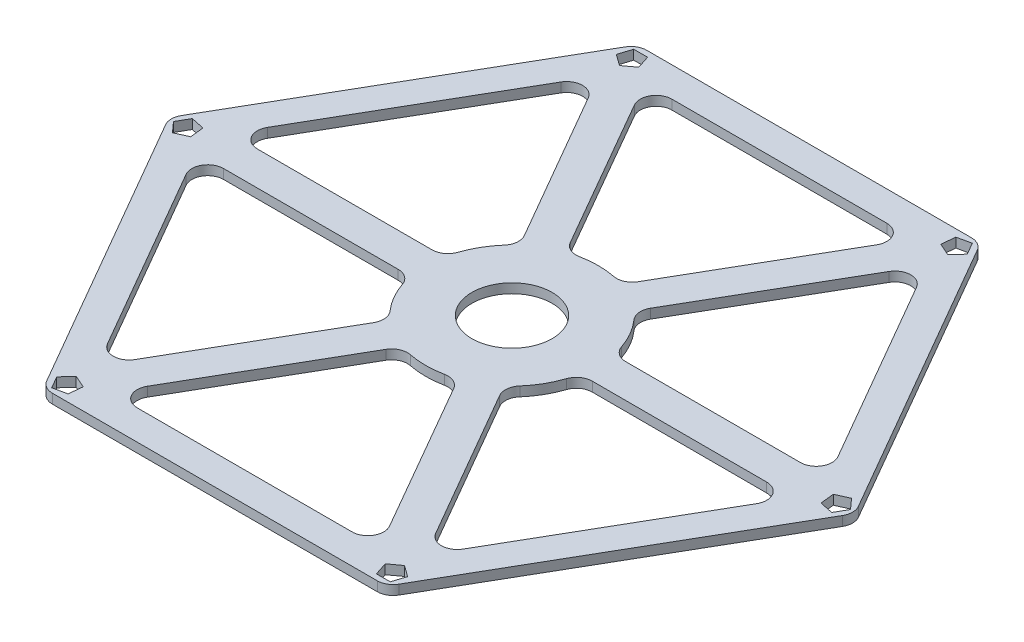
SolidWorks part; units mm, degrees
ref_plane "Front Plane" through (0, 0, 0) normal (0, 0, 1) x (1, 0, 0)
ref_plane "Top Plane" through (0, 0, 0) normal (0, 1, 0) x (1, 0, 0)
ref_plane "Right Plane" through (0, 0, 0) normal (1, 0, 0) x (0, 0, -1)
sketch "Sketch1" plane through (0, 0, 0) normal (0, 1, 0) x (1, 0, 0)
  line L0 (-30.85, 53.4338) -> (-30.85, 42.7905) construction
  line L1 (-32.5, 56.2917) -> (-65, 0)
  line L2 (-65, 0) -> (-32.5, -56.2917)
  line L3 (-32.5, -56.2917) -> (32.5, -56.2917)
  line L4 (32.5, -56.2917) -> (65, 0)
  line L5 (65, 0) -> (32.5, 56.2917)
  line L6 (32.5, 56.2917) -> (-32.5, 56.2917)
  line L7 (-31.0984, 47.4555) -> (-56.6469, 3.2043)
  line L8 (-56.6469, -3.2043) -> (-31.0984, -47.4555)
  line L9 (-25.5484, -50.6598) -> (3, -50.6598)
  line L10 (31.0984, -47.4555) -> (56.6468, -3.2044)
  line L11 (56.6469, 3.2043) -> (31.0985, 47.4554)
  line L12 (25.5484, 50.6598) -> (-25.5483, 50.6598)
  line L13 (-30.85, 53.4338) -> (-61.7, 0) construction
  line L14 (-61.7, 0) -> (-30.85, -53.4338) construction
  line L15 (-30.85, -53.4338) -> (30.85, -53.4338) construction
  line L16 (30.85, -53.4338) -> (61.7, 0) construction
  line L17 (61.7, 0) -> (30.85, 53.4338) construction
  line L18 (30.85, 53.4338) -> (-30.85, 53.4338) construction
  line L50 (28.9265, 52.3155) -> (31.3192, 51.2589)
  line L51 (-30.8433, 51.2089) -> (-28.7319, 52.7526)
  line L52 (-28.7319, 52.7526) -> (-29.5477, 55.2377)
  line L58 (-31.0984, 47.4555) -> (-10.8026, 12.302)
  line L60 (25.5484, 50.6598) -> (5.2525, 15.5063)
  line L66 (56.6469, 3.2043) -> (16.0551, 3.2043)
  line L72 (31.0984, -47.4555) -> (10.8026, -12.302)
  line L78 (-25.5484, -50.6598) -> (-5.2525, -15.5063)
  line L84 (-56.6469, -3.2043) -> (-16.0551, -3.2043)
  line L89 (-5.298, 15.4908) -> (-25.5483, 50.6598)
  line L91 (-29.5477, 55.2377) -> (-32.1632, 55.2298)
  line L92 (10.7664, 12.3336) -> (31.0985, 47.4554)
  line L94 (-32.1632, 55.2298) -> (-32.9639, 52.7398)
  line L95 (16.0644, -3.1572) -> (56.6468, -3.2044)
  line L97 (-32.9639, 52.7398) -> (-30.8433, 51.2089)
  line L98 (5.298, -15.4908) -> (25.5483, -50.6598)
  line L100 (31.3192, 51.2589) -> (33.0634, 53.2079)
  line L101 (-10.8026, -12.302) -> (-31.0984, -47.4555)
  line L103 (33.0634, 53.2079) -> (31.7488, 55.4691)
  line L104 (-16.0551, 3.2043) -> (-56.6469, 3.2043)
  line L106 (31.7488, 55.4691) -> (29.1921, 54.9175)
  line L107 (29.1921, 54.9175) -> (28.9265, 52.3155)
  line L108 (59.7698, 1.1066) -> (60.0511, -1.4938)
  line L109 (60.0511, -1.4938) -> (62.6111, -2.0298)
  line L110 (62.6111, -2.0298) -> (63.912, 0.2393)
  line L111 (63.912, 0.2393) -> (62.156, 2.1777)
  line L112 (62.156, 2.1777) -> (59.7698, 1.1066)
  line L113 (30.8433, -51.2089) -> (28.7319, -52.7526)
  line L114 (28.7319, -52.7526) -> (29.5477, -55.2377)
  line L115 (29.5477, -55.2377) -> (32.1632, -55.2298)
  line L116 (32.1632, -55.2298) -> (32.9639, -52.7398)
  line L117 (32.9639, -52.7398) -> (30.8433, -51.2089)
  line L118 (-28.9265, -52.3155) -> (-31.3192, -51.2589)
  line L119 (-31.3192, -51.2589) -> (-33.0634, -53.2079)
  line L120 (-33.0634, -53.2079) -> (-31.7488, -55.4691)
  line L121 (-31.7488, -55.4691) -> (-29.1921, -54.9175)
  line L122 (-29.1921, -54.9175) -> (-28.9265, -52.3155)
  line L123 (-59.7698, -1.1066) -> (-60.0511, 1.4938)
  line L124 (-60.0511, 1.4938) -> (-62.6111, 2.0298)
  line L125 (-62.6111, 2.0298) -> (-63.912, -0.2393)
  line L126 (-63.912, -0.2393) -> (-62.156, -2.1777)
  line L127 (-62.156, -2.1777) -> (-59.7698, -1.1066)
  line L128 (0, 0) -> (0, -56.2917) construction
  line L134 (3, -50.6598) -> (25.5483, -50.6598)
  circle A0 centre (0, 0) radius 56.2917 construction
  circle A1 centre (0, 0) radius 50.6598 construction
  circle A2 centre (0, 0) radius 53.4338 construction
  circle A3 centre (-30.85, 53.4338) radius 1.8 construction
  arc A4 (-10.8026, 12.302) -> (-16.0551, 3.2043) centre (0, 0) ccw
  arc A5 (5.2525, 15.5063) -> (-5.298, 15.4908) centre (0, 0) ccw
  arc A6 (16.0551, 3.2043) -> (10.7664, 12.3336) centre (0, 0) ccw
  arc A7 (10.8026, -12.302) -> (16.0644, -3.1572) centre (0, 0) ccw
  arc A8 (-5.2525, -15.5063) -> (3.0697, -16.0814) centre (0, 0) ccw
  arc A9 (-16.0551, -3.2043) -> (-10.8026, -12.302) centre (0, 0) ccw
  arc A10 (3.0697, -16.0814) -> (5.298, -15.4908) centre (0, 0) ccw
  point P53 (0, 0)
  point P58 (-0.0078, -0.0152)
  point P70 (0, 0)
  point P87 (0, 0)
  dimension "D1" = 65
  dimension "D2" = 30
  dimension "D3" = 3.3
  dimension "D4" = 6
  dimension "D7" = 6
extrude "Boss-Extrude1" add sketch "Sketch1" along normal blind 1.8
fillet "Fillet1" radius 3 6 edges at (-65, 0.9, 0) (-32.5, 0.9, 56.2917) (32.5, 0.9, 56.2917) (65, 0.9, 0) (32.5, 0.9, -56.2917) (-32.5, 0.9, -56.2917)
sketch "Sketch2" plane through (0, 0, 0) normal (0, 1, 0) x (1, 0, 0)
fillet "Fillet2" radius 3 24 edges at (-25.5484, 0.9, 50.6598) (31.0984, 0.9, 47.4555) (25.5483, 0.9, 50.6598) (-31.0984, 0.9, 47.4555) (-56.6469, 0.9, 3.2043) (-16.0551, 0.9, 3.2043) (-10.8026, 0.9, 12.302) (-31.0984, 0.9, -47.4555) (-56.6469, 0.9, -3.2043) (-16.0551, 0.9, -3.2043) (-10.8026, 0.9, -12.302) (-25.5483, 0.9, -50.6598) (25.5484, 0.9, -50.6598) (56.6469, 0.9, -3.2043) (56.6468, 0.9, 3.2044) (31.0985, 0.9, -47.4554) (-5.2525, 0.9, 15.5063) (5.298, 0.9, 15.4908) (10.8026, 0.9, 12.302) (16.0644, 0.9, 3.1572) (16.0551, 0.9, -3.2043) (10.7664, 0.9, -12.3336) (5.2525, 0.9, -15.5063) (-5.298, 0.9, -15.4908)
ref_plane "Plane1" through (0, 3.6, 0) normal (0, 1, 0) x (1, 0, 0)
sketch "Sketch3" plane through (0, 3.6, 0) normal (0, 1, 0) x (1, 0, 0)
  circle A0 centre (0, 0) radius 7.6
extrude "Cut-Extrude1" cut sketch "Sketch3" against normal blind 10
ref_plane "Plane2" through (0, 1.8, 0) normal (0, 1, 0) x (1, 0, 0)
ref_plane "Plane3" through (0, 0, 0) normal (0, -1, 0) x (-1, 0, 0)
sketch "Sketch5" plane through (0, 0, 0) normal (0, -1, 0) x (-1, 0, 0)
  line L5 (21.5, -37.4) -> (-21.5, 37.4) construction
  line L6 (21.5, 37.4) -> (-21.5, -37.4) construction
  point P0 (0, 0)
  dimension "D1" = 43
  dimension "D2" = 74.8
scale "Scale1" scale about centroid uniform scaling yes scale factor 1.15
